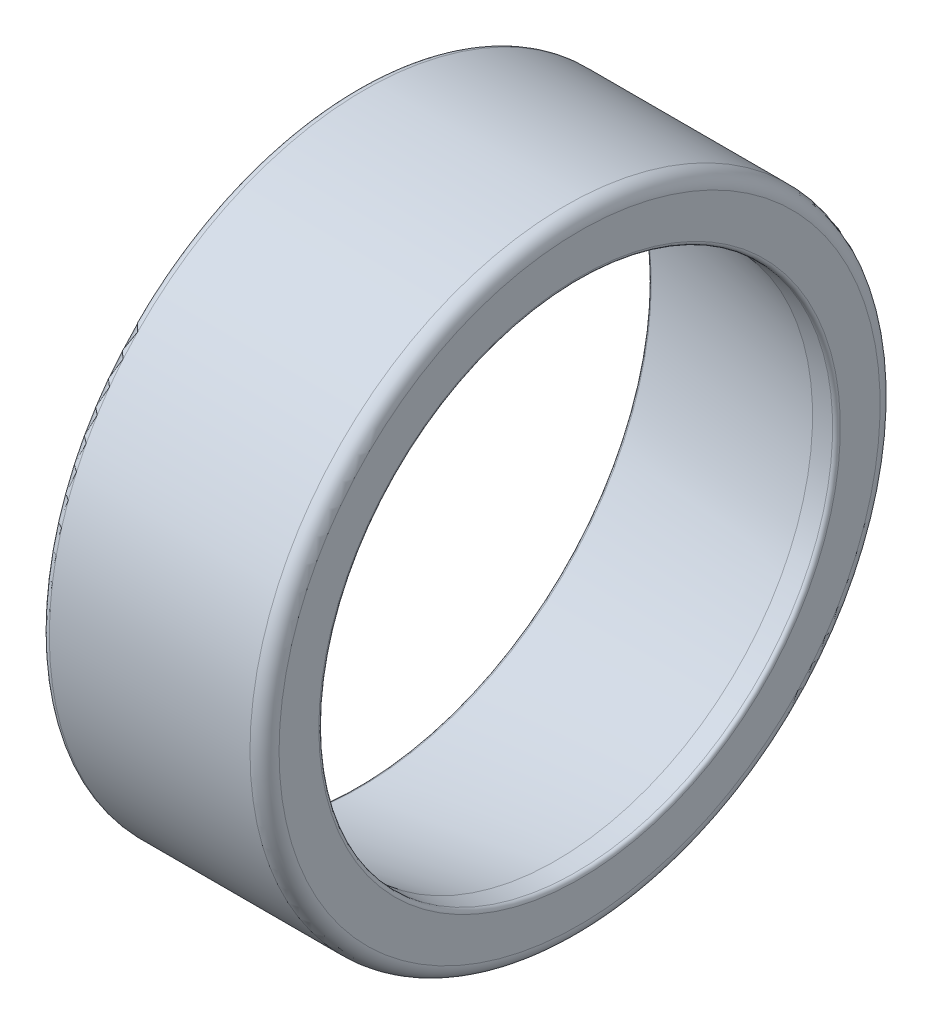
SolidWorks part; units mm, degrees
ref_plane "Front Plane" through (0, 0, 0) normal (0, 0, 1) x (1, 0, 0)
ref_plane "Top Plane" through (0, 0, 0) normal (0, 1, 0) x (1, 0, 0)
ref_plane "Right Plane" through (0, 0, 0) normal (1, 0, 0) x (0, 0, -1)
sketch "Sketch1" plane through (0, 0, 0) normal (0, 0, 1) x (1, 0, 0)
  line L0 (0, 0) -> (21, 0) construction
  line L1 (3.4, 37.5505) -> (3.4, 18.8856) construction
  line L2 (0, 37.5505) -> (3.4, 37.5505) construction
  line L3 (0, 37.5505) -> (0, 27.5) construction
  line L4 (0, 27.5) -> (21, 27.5) construction
  line L5 (21, 17.577) -> (21, 27.5) construction
  line L6 (2.0778, 27.5468) -> (20.2251, 24.3469) construction
  line L7 (22, 26.5) -> (22, 32.5)
  line L8 (22, 32.5) -> (-1, 32.5)
  line L9 (-1, 30.1203) -> (-1, 32.5)
  line L10 (3.4, 18.8856) -> (18.3572, 17.577) construction
  line L11 (-1, 30.1203) -> (19.5319, 26.5)
  line L12 (4.0729, 23.9964) -> (18.9445, 22.0385) construction
  line L13 (3.4, 18.8856) -> (4.7457, 29.1072) construction
  line L14 (18.3572, 17.577) -> (19.5319, 26.5) construction
  line L15 (18.3572, 17.577) -> (21, 17.577) construction
  line L16 (23.2, 20.8016) -> (23.2, 18.577) construction
  line L17 (1.8, 25.9711) -> (19.9473, 22.7712) construction
  line L18 (21.6, 20.8016) -> (21.6, 18.577) construction
  line L19 (21.6, 18.577) -> (23.2, 18.577) construction
  line L20 (1.8, 25.9711) -> (2.0778, 27.5468) construction
  line L21 (19.5319, 26.5) -> (22, 26.5)
  arc A0 (19.9473, 22.7712) -> (21.6, 20.8016) centre (19.6, 20.8016) cw construction
  arc A1 (20.2251, 24.3469) -> (23.2, 20.8016) centre (19.6, 20.8016) cw construction
  dimension "D14" = 2
  dimension "D15" = 3.6
  dimension "D1" = 21
  dimension "D2" = 27.5
  dimension "D3" = 32.5
  dimension "D4" = 1
  dimension "D5" = 23
  dimension "D6" = 5
  dimension "D7" = 1.8
  dimension "D8" = 2.5
  dimension "D9" = 15
  dimension "D10" = 9
  dimension "D11" = 2
  dimension "D12" = 1.6
  dimension "D13" = 1.6
  dimension "D16" = 0.6
  dimension "D17" = 1
  dimension "D18" = 3.4
  dimension "D19" = 5
  dimension "D20" = 6
  dimension "D21" = 24.3469
revolve "Revolve1" add sketch "Sketch1" angle 360 about L0
fillet "Fillet1" radius 1.5 1 edges at (22, 0, 32.5)
fillet "Fillet2" radius 0.8 1 edges at (-1, 0, 32.5)
fillet "Fillet3" radius 0.4 2 edges at (-1, 0, 30.1203) (22, 0, 26.5)
